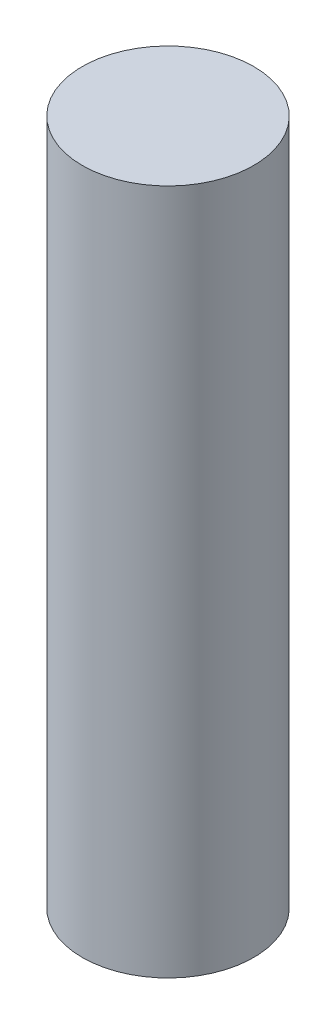
SolidWorks part; units mm, degrees
ref_plane "Front Plane" through (0, 0, 0) normal (0, 0, 1) x (1, 0, 0)
ref_plane "Top Plane" through (0, 0, 0) normal (0, 1, 0) x (1, 0, 0)
ref_plane "Right Plane" through (0, 0, 0) normal (1, 0, 0) x (0, 0, -1)
sketch "Sketch1" plane through (0, 0, 0) normal (0, 1, 0) x (1, 0, 0)
  circle A0 centre (0, 0) radius 6.35
  dimension "D1" = 12.7
extrude "Boss-Extrude1" add sketch "Sketch1" along normal blind 50.8
